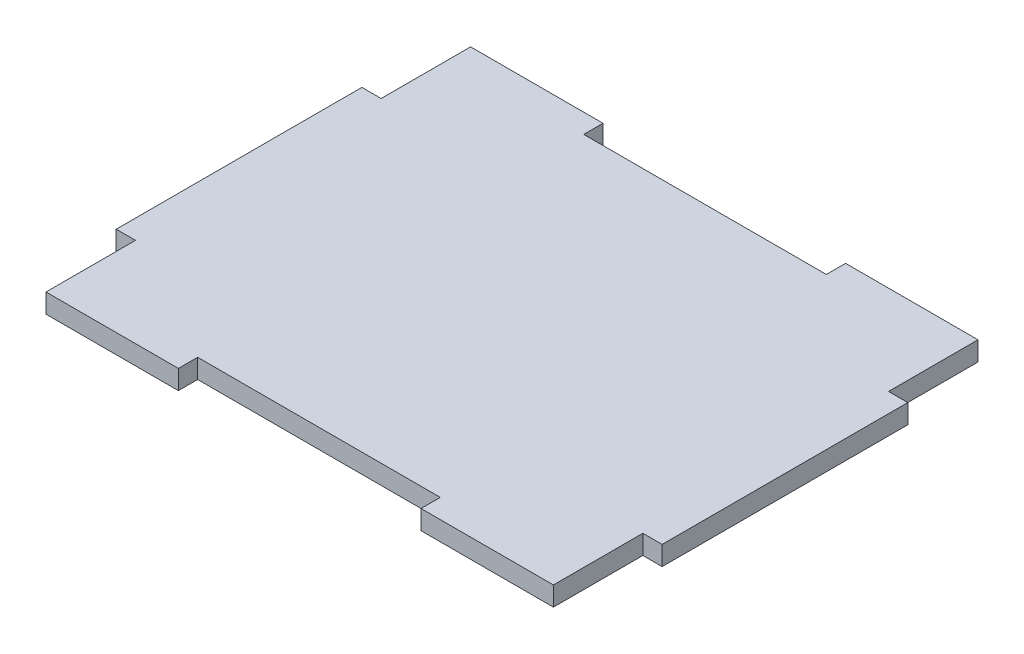
SolidWorks part; units mm, degrees
ref_plane "Front Plane" through (0, 0, 0) normal (0, 0, 1) x (1, 0, 0)
ref_plane "Top Plane" through (0, 0, 0) normal (0, 1, 0) x (1, 0, 0)
ref_plane "Right Plane" through (0, 0, 0) normal (1, 0, 0) x (0, 0, -1)
sketch "Sketch1" plane through (0, 0, 0) normal (0, 1, 0) x (1, 0, 0)
  line L0 (-41.825, 31.825) -> (41.825, 31.825)
  line L1 (-45, -35) -> (45, -35)
  line L2 (-45, -35) -> (-45, 35)
  line L3 (-45, 35) -> (45, 35)
  line L4 (45, -35) -> (45, 35)
  line L5 (-45, -35) -> (45, 35) construction
  line L6 (-45, 35) -> (45, -35) construction
  line L7 (41.825, -35) -> (41.825, 35)
  line L8 (-41.825, -31.825) -> (41.825, -31.825)
  line L9 (-41.825, -35) -> (-41.825, 35)
  line L10 (-41.825, -31.825) -> (-41.825, 31.825) construction
  line L11 (-20, 38.175) -> (20, 38.175)
  line L12 (-20, 38.175) -> (-20, 31.825)
  line L13 (-20, 31.825) -> (20, 31.825)
  line L14 (20, 38.175) -> (20, 31.825)
  line L15 (-20, 38.175) -> (20, 31.825) construction
  line L16 (-20, 31.825) -> (20, 38.175) construction
  line L17 (-20, -38.175) -> (20, -38.175)
  line L18 (-20, -38.175) -> (-20, -31.825)
  line L19 (-20, -31.825) -> (20, -31.825)
  line L20 (20, -38.175) -> (20, -31.825)
  line L21 (-20, -38.175) -> (20, -31.825) construction
  line L22 (-20, -31.825) -> (20, -38.175) construction
  line L23 (-48.175, -20.25) -> (-41.825, -20.25)
  line L24 (-48.175, -20.25) -> (-48.175, 20.25)
  line L25 (-48.175, 20.25) -> (-41.825, 20.25)
  line L26 (-41.825, -20.25) -> (-41.825, 20.25)
  line L27 (-48.175, -20.25) -> (-41.825, 20.25) construction
  line L28 (-48.175, 20.25) -> (-41.825, -20.25) construction
  line L29 (48.175, -20.25) -> (41.825, -20.25)
  line L30 (48.175, -20.25) -> (48.175, 20.25)
  line L31 (48.175, 20.25) -> (41.825, 20.25)
  line L32 (41.825, -20.25) -> (41.825, 20.25)
  line L33 (48.175, -20.25) -> (41.825, 20.25) construction
  line L34 (48.175, 20.25) -> (41.825, -20.25) construction
  line L35 (41.825, -31.825) -> (41.825, 31.825) construction
  point P0 (0, 0)
  point P10 (0, 35)
  point P15 (0, -35)
  point P20 (-45, 0)
  point P25 (45, 0)
  dimension "D1" = 70
  dimension "D2" = 90
  dimension "D4" = 40
  dimension "D5" = 40.5
  dimension "D3" = 3.175
extrude "Boss-Extrude1" add sketch "Sketch1" along normal blind 3.175 contours L9 L8 L7 L0 | L1 L18 L8 L9 | L20 L1 L7 L8 | L4 L31 L7 L29 | L3 L14 L0 L7 | L12 L3 L9 L0 | L25 L2 L23 L9
